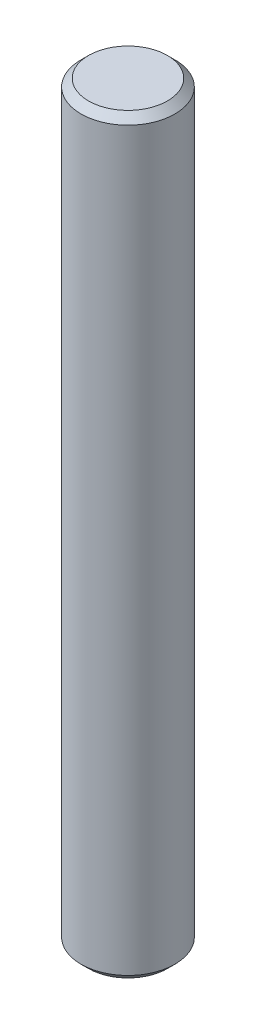
SolidWorks part; units mm, degrees
ref_plane "Front Plane" through (0, 0, 0) normal (0, 0, 1) x (1, 0, 0)
ref_plane "Top Plane" through (0, 0, 0) normal (0, 1, 0) x (1, 0, 0)
ref_plane "Right Plane" through (0, 0, 0) normal (1, 0, 0) x (0, 0, -1)
sketch "Sketch1" plane through (0, 0, 0) normal (0, 1, 0) x (1, 0, 0)
  circle A0 centre (0, 0) radius 12.5
  dimension "D1" = 25
extrude "Boss-Extrude1" add sketch "Sketch1" along normal mid plane 200
chamfer "Chamfer1" distance 2 angle 45 2 edges at (0, -100, 12.5) (0, 100, 12.5)
